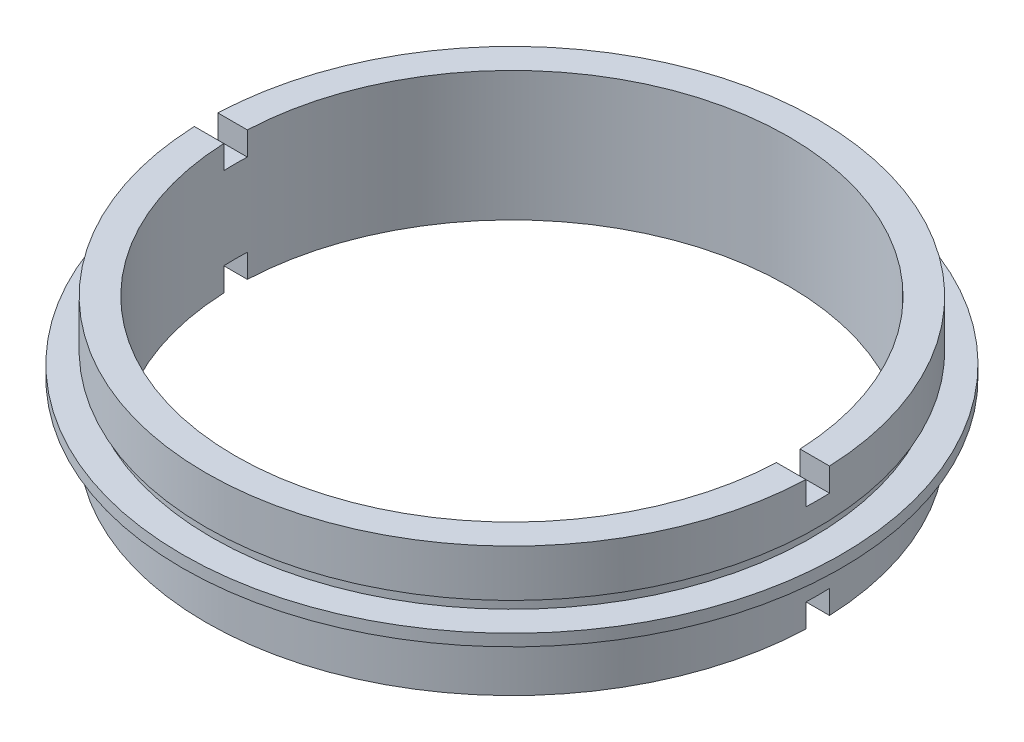
SolidWorks part; units mm, degrees
ref_plane "前视基准面" through (0, 0, 0) normal (0, 0, 1) x (1, 0, 0)
ref_plane "上视基准面" through (0, 0, 0) normal (0, 1, 0) x (1, 0, 0)
ref_plane "右视基准面" through (0, 0, 0) normal (1, 0, 0) x (0, 0, -1)
sketch "草图1" plane through (0, 0, 0) normal (0, 0, 1) x (1, 0, 0)
  line L0 (0, 22.6775) -> (0, 0) construction
  line L1 (-23.5, 11) -> (-26, 11)
  line L2 (-26, 11) -> (-26, 7)
  line L3 (-26, 7) -> (-25.5, 7)
  line L4 (-25.5, 7) -> (-25.5, 6)
  line L5 (-25.5, 6) -> (-28, 6)
  line L6 (-28, 6) -> (-28, 5)
  line L7 (-28, 5) -> (-25.5, 5)
  line L8 (-25.5, 5) -> (-25.5, 4)
  line L9 (-25.5, 4) -> (-26, 4)
  line L10 (-26, 4) -> (-26, 0)
  line L11 (-26, 0) -> (-23.5, 0)
  line L12 (-23.5, 0) -> (-23.5, 11)
  point P5 (-28, 5.5)
  dimension "D1" = 11
  dimension "D2" = 1
  dimension "D3" = 1
  dimension "D4" = 5
  dimension "D5" = 5
  dimension "D6" = 26
  dimension "D7" = 28
  dimension "D8" = 26
  dimension "D9" = 25.5
  dimension "D10" = 25.5
  dimension "D11" = 23.5
  dimension "D12" = 0
revolve "旋转1" add sketch "草图1" angle 360 about L0
cosmetic thread "装饰螺纹线1" parameters "D2"=51
cosmetic thread "装饰螺纹线2" parameters "D2"=51
cosmetic thread "装饰螺纹线3" parameters "D2"=48
sketch "草图2" plane through (0, 0, 0) normal (1, 0, 0) x (0, 0, -1)
  line L0 (23.5, 11) -> (-23.5, 11) construction
  line L1 (-1, 13.594) -> (1, 13.594)
  line L2 (-1, 13.594) -> (-1, 9)
  line L3 (-1, 9) -> (1, 9)
  line L4 (1, 13.594) -> (1, 9)
  line L5 (-1, 2) -> (1, 2)
  line L6 (-1, 2) -> (-1, -4.6679)
  line L7 (-1, -4.6679) -> (1, -4.6679)
  line L8 (1, 2) -> (1, -4.6679)
  dimension "D1" = 2
  dimension "D2" = 1
  dimension "D3" = 2
  dimension "D4" = 1
  dimension "D5" = 2
  dimension "D6" = 2
extrude "切除-拉伸1" cut sketch "草图2" against normal mid plane 79
